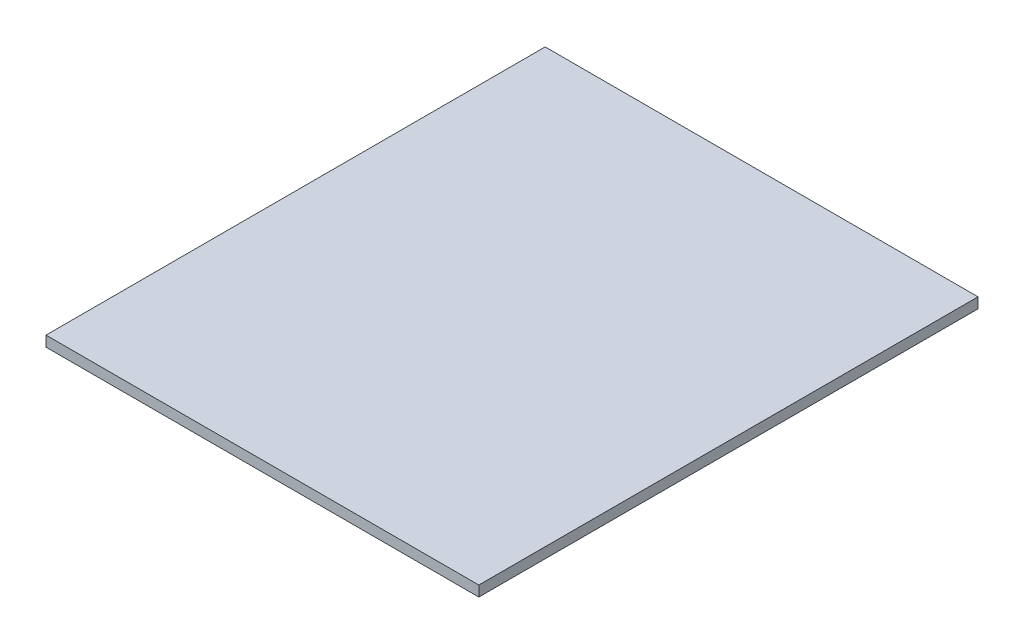
SolidWorks part; units mm, degrees
ref_plane "Front" through (0, 0, 0) normal (0, 0, 1) x (1, 0, 0)
ref_plane "Top" through (0, 0, 0) normal (0, 1, 0) x (1, 0, 0)
ref_plane "Right" through (0, 0, 0) normal (1, 0, 0) x (0, 0, -1)
sketch "Sketch1" plane through (0, 0, 0) normal (0, 1, 0) x (1, 0, 0)
  line L1 (0, 0) -> (248.0112, 0)
  line L2 (0, 0) -> (0, 286.0056)
  line L3 (0, 286.0056) -> (248.0112, 286.0056)
  line L4 (248.0112, 0) -> (248.0112, 286.0056)
  dimension "D1" = 248.0112
  dimension "D2" = 286.0056
extrude "Boss-Extrude1" add sketch "Sketch1" along normal blind 5.9944
sketch "Sketch3" [suppressed] plane through (0, 5.9944, 0) normal (0, 1, 0) x (1, 0, 0)
  line L0 (248.0112, 286.0056) -> (0, 286.0056) construction
  line L1 (124.0056, 286.0056) -> (124.0056, 0) construction
  line L3 (0, 0) -> (248.0112, 0) construction
  circle A0 centre (124.0056, 246.8256) radius 7.5
  circle A1 centre (124.0056, 33.08) radius 7.5
  point P4 (124.0056, 286.0056)
  dimension "D2" = 15
  dimension "D1" = 39.18
  dimension "D3" = 33.08
extrude "Cut-Extrude1" [suppressed] cut sketch "Sketch3" against normal through all
equation "\"ABS_thickness_1/16\" = 1.524\t"
equation "\"ABS_thickness_3/32\" = 2.3622"
equation "\"ABS_thickness_1/8\" = 2.9972\t"
equation "\"ABS_thickness_1/4\" = 5.9944"
equation "\"Bus_bar_thickness\" = 3.175"
equation "\"Connector_width\" = 20.2"
equation "\"Number_of_cells_long\" = 25"
equation "\"Number_of_cells_wide\" = 2"
equation "\"Cell_height\" = 65.0"
equation "\"Cell_diam\" = 18.0"
equation "\"Enclosure_Width\" = 292"
equation "\"Enclosure_Length\" = 260"
equation "\"Enclosure_Height\" = 515"
equation "\"D1@Sketch1\"=\"Enclosure_Length\"-2*\"ABS_thickness_1/4\""
equation "\"D2@Sketch1\"=\"Enclosure_Width\"-(2*\"ABS_thickness_1/8\")"
